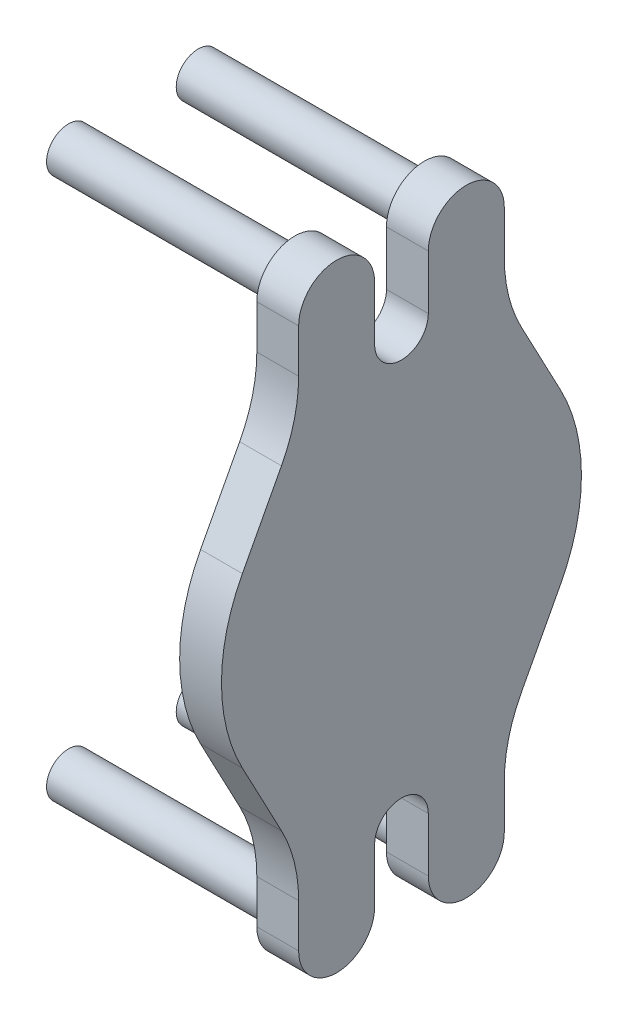
SolidWorks part; units mm, degrees
ref_plane "Front Plane" through (0, 0, 0) normal (0, 0, 1) x (1, 0, 0)
ref_plane "Top Plane" through (0, 0, 0) normal (0, 1, 0) x (1, 0, 0)
ref_plane "Right Plane" through (0, 0, 0) normal (1, 0, 0) x (0, 0, -1)
sketch "Sketch1" plane through (0, 0, 0) normal (0, 0, 1) x (1, 0, 0)
  line L0 (8.255, 0) -> (-8.255, 0) construction
  line L1 (25.4, 0) -> (-25.4, 0) construction
  line L2 (8.255, 0) -> (8.255, 18.25)
  line L3 (8.255, 18.25) -> (25.4, 18.25)
  line L4 (25.4, 18.25) -> (25.4, 0)
  line L5 (8.255, 0) -> (25.4, 0)
  point P4 (0, 0)
  point P8 (0, 0)
  dimension "D1" = 16.51
  dimension "D2" = 50.8
  dimension "D3" = 18.25
revolve "Revolve1" add sketch "Sketch1" angle 360 about L5
sketch "Sketch2" plane through (8.255, 0, 0) normal (-1, 0, 0) x (0, 0, 1)
  circle A0 centre (0, 0) radius 3.7147
  dimension "D1" = 7.4295
extrude "Cut-Extrude1" cut sketch "Sketch2" against normal blind 8.5725
sketch "Sketch3" plane through (25.4, 0, 0) normal (1, 0, 0) x (0, 0, -1)
  line L0 (-20.8953, -55) -> (-20.8953, -46.1532)
  line L1 (13.175, -55) -> (-13.175, -55) construction
  line L2 (13.175, -55) -> (13.175, 55) construction
  line L3 (13.175, 55) -> (-13.175, 55) construction
  line L4 (-13.175, -55) -> (-13.175, 55) construction
  line L5 (13.175, -55) -> (-13.175, 55) construction
  line L6 (13.175, 55) -> (-13.175, -55) construction
  line L7 (-24.3823, -32.1152) -> (-32.3245, -17.1152)
  line L9 (-5.4548, -55) -> (-5.4548, -44)
  line L11 (5.4547, -44) -> (5.4547, -55)
  line L12 (20.8953, -55) -> (20.8953, -46.1532)
  line L13 (24.3823, -32.1152) -> (32.3245, -17.1152)
  line L14 (28.6, 0) -> (-28.6, 0) construction
  line L15 (13.175, -55) -> (-13.175, 55) construction
  line L16 (13.175, 55) -> (-13.175, -55) construction
  line L17 (13.175, 55) -> (-13.175, 55) construction
  line L18 (24.3823, 32.1152) -> (32.3245, 17.1152)
  line L19 (20.8953, 55) -> (20.8953, 46.1532)
  line L20 (5.4547, 44) -> (5.4547, 55)
  line L21 (-5.4548, 55) -> (-5.4548, 44)
  line L22 (-24.3823, 32.1152) -> (-32.3245, 17.1152)
  line L23 (-20.8953, 55) -> (-20.8953, 46.1532)
  arc A15 (32.3245, -17.1152) -> (32.3245, 17.1152) centre (0, 0) ccw
  arc A16 (-5.4548, 55) -> (-20.8953, 55) centre (-13.175, 55) ccw
  arc A17 (-20.8953, -55) -> (-5.4548, -55) centre (-13.175, -55) ccw
  arc A18 (5.4547, -55) -> (20.8953, -55) centre (13.175, -55) ccw
  arc A19 (20.8953, 55) -> (5.4547, 55) centre (13.175, 55) ccw
  arc A20 (-5.4548, -44) -> (5.4547, -44) centre (0, -44) cw
  arc A21 (20.8953, -46.1532) -> (24.3823, -32.1152) centre (50.8953, -46.1532) cw
  arc A22 (-20.8953, -46.1532) -> (-24.3823, -32.1152) centre (-50.8953, -46.1532) ccw
  arc A23 (-20.8953, 46.1532) -> (-24.3823, 32.1152) centre (-50.8953, 46.1532) cw
  arc A24 (20.8953, 46.1532) -> (24.3823, 32.1152) centre (50.8953, 46.1532) ccw
  arc A25 (-5.4548, 44) -> (5.4547, 44) centre (0, 44) ccw
  arc A26 (5.4547, 55) -> (20.8953, 55) centre (13.175, 55) cw
  arc A27 (-20.8953, 55) -> (-5.4548, 55) centre (-13.175, 55) cw
  arc A29 (-32.3245, 17.1152) -> (-32.3245, -17.1152) centre (0, 0) ccw
  circle M2 centre (0, 0) radius 18.25
  dimension "D3" = 15.4405
  dimension "D5" = 7.7203
  dimension "D4" = 30
  dimension "D7" = 15
  dimension "D9" = 110
  dimension "D1" = 73.152
  dimension "D6" = 15
  dimension "D2" = 26.35
  dimension "D8" = 11
extrude "Boss-Extrude1" add sketch "Sketch3" along normal blind 8.5 separate body contours L22 A29 L7 A22 L0 A17 L9 A20 L11 A18 L12 A21 L13 A15 L18 A24 L19 A19 L20 A25 L21 A16 L23 A23 M2 | M2
sketch "Sketch4" plane through (25.4, 0, 0) normal (-1, 0, 0) x (0, 0, 1)
  line L1 (13.175, -55) -> (-13.175, -55) construction
  line L2 (13.175, -55) -> (13.175, 55) construction
  line L3 (13.175, 55) -> (-13.175, 55) construction
  line L4 (-13.175, -55) -> (-13.175, 55) construction
  line L5 (13.175, -55) -> (-13.175, 55) construction
  line L6 (13.175, 55) -> (-13.175, -55) construction
  circle A0 centre (-13.175, 55) radius 4.45
  circle A1 centre (13.175, -55) radius 4.45
  circle A2 centre (13.175, 55) radius 4.45
  circle A3 centre (-13.175, -55) radius 4.45
  point P6 (0, 0)
  dimension "D1" = 8.9
extrude "Boss-Extrude2" add sketch "Sketch4" along normal blind 46
sketch "Sketch5" plane through (8.255, 0, 0) normal (-1, 0, 0) x (0, 0, 1)
  circle A0 centre (0, 0) radius 18.25
  dimension "D1" = 36.5
extrude "Cut-Extrude2" cut sketch "Sketch5" against normal blind 22.15
